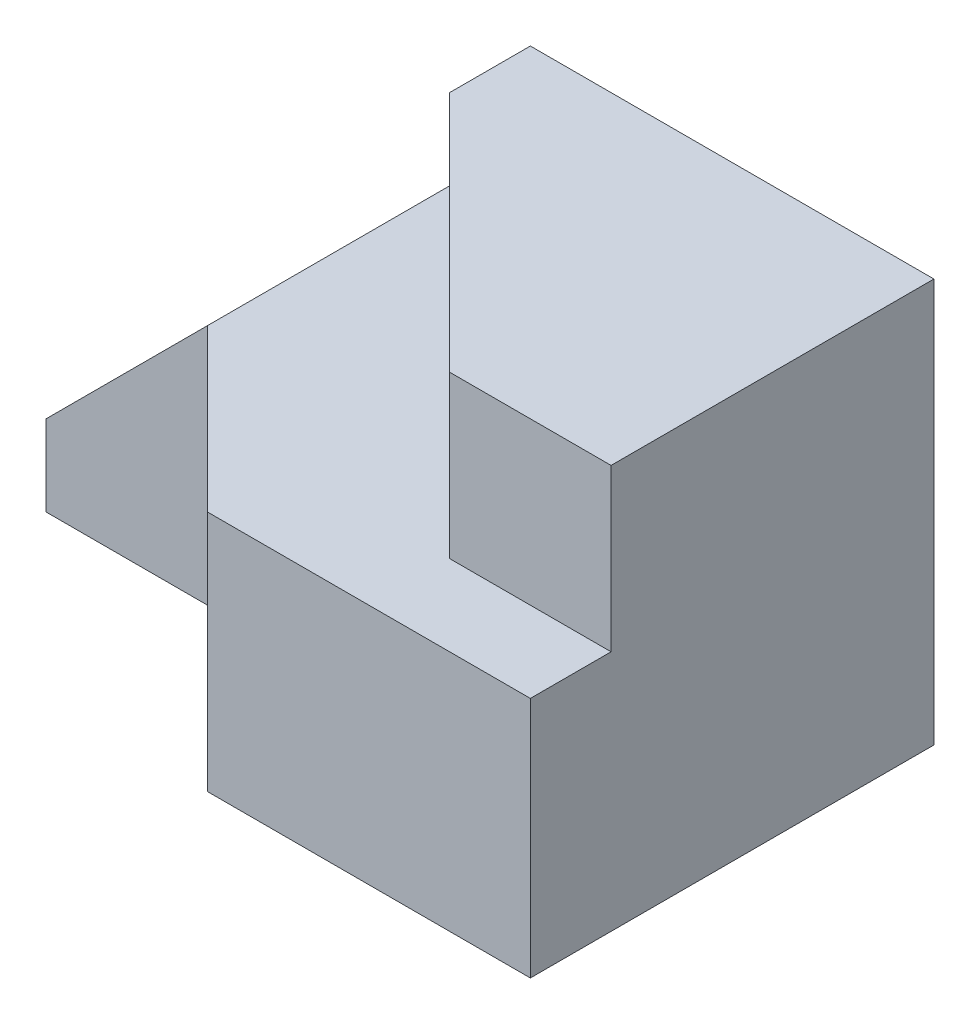
SolidWorks part; units mm, degrees
ref_plane "Front Plane" through (0, 0, 0) normal (0, 0, 1) x (1, 0, 0)
ref_plane "Top Plane" through (0, 0, 0) normal (0, 1, 0) x (1, 0, 0)
ref_plane "Right Plane" through (0, 0, 0) normal (1, 0, 0) x (0, 0, -1)
sketch "Sketch1" plane through (0, 0, 0) normal (0, 1, 0) x (1, 0, 0)
  line L1 (0, 0) -> (60, 0)
  line L2 (0, 0) -> (0, 50)
  line L3 (0, 50) -> (60, 50)
  line L4 (60, 0) -> (60, 50)
  dimension "D1" = 60
  dimension "D2" = 50
extrude "Boss-Extrude1" add sketch "Sketch1" along normal blind 30
sketch "Sketch2" plane through (0, 30, 0) normal (0, 1, 0) x (1, 0, 0)
  line L0 (0, 20) -> (20, 0)
  line L1 (0, 50) -> (0, 0) construction
  line L2 (0, 0) -> (60, 0) construction
  line L3 (20, 0) -> (0, 0)
  line L4 (0, 0) -> (0, 20)
  dimension "D1" = 20
  dimension "D2" = 20
extrude "Cut-Extrude1" cut sketch "Sketch2" against normal blind 30
sketch "Sketch3" plane through (0, 30, 0) normal (0, 1, 0) x (1, 0, 0)
  line L0 (10, 50) -> (60, 50)
  line L1 (60, 50) -> (0, 50) construction
  line L2 (60, 50) -> (60, 10)
  line L3 (60, 0) -> (60, 50) construction
  line L4 (60, 10) -> (40, 10)
  line L5 (40, 10) -> (10, 40)
  line L6 (10, 40) -> (10, 50)
  dimension "D1" = 10
  dimension "D2" = 10
  dimension "D3" = 40
  dimension "D4" = 20
extrude "Boss-Extrude2" add sketch "Sketch3" along normal blind 20
sketch "Sketch4" plane through (0, 0, -50) normal (0, 0, -1) x (-1, 0, 0)
  line L0 (20, 10) -> (0, 30)
  line L1 (0, 0) -> (20, 0)
  line L2 (0, 0) -> (0, 30)
  line L3 (0, 30) -> (20, 30)
  line L4 (20, 0) -> (20, 30)
  line M2 (0, 0) -> (0, 30)
  dimension "D1" = 20
  dimension "D2" = 30
  dimension "D3" = 10
extrude "Boss-Extrude3" add sketch "Sketch4" against normal blind 30 contours L1 L4 L0 M2
